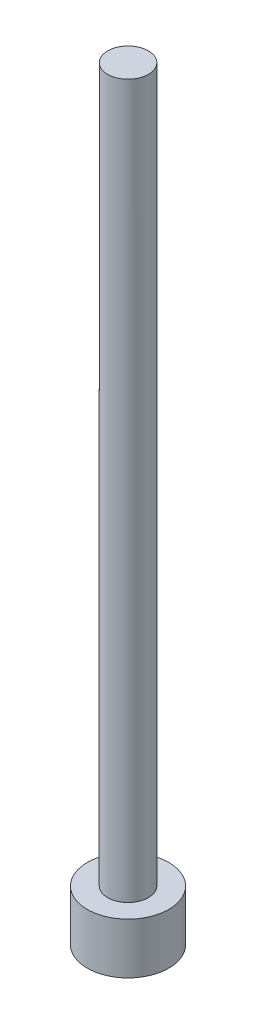
SolidWorks part; units mm, degrees
ref_plane "Front Plane" through (0, 0, 0) normal (0, 0, 1) x (1, 0, 0)
ref_plane "Top Plane" through (0, 0, 0) normal (0, 1, 0) x (1, 0, 0)
ref_plane "Right Plane" through (0, 0, 0) normal (1, 0, 0) x (0, 0, -1)
sketch "Sketch1" plane through (0, 0, 0) normal (0, 1, 0) x (1, 0, 0)
  circle A0 centre (0, 0) radius 4
extrude "Boss-Extrude1" add sketch "Sketch1" along normal blind 150
sketch "Sketch2" plane through (0, 0, 0) normal (0, -1, 0) x (1, 0, 0)
  circle A0 centre (0, 0) radius 8
extrude "Boss-Extrude2" add sketch "Sketch2" against normal blind 10
